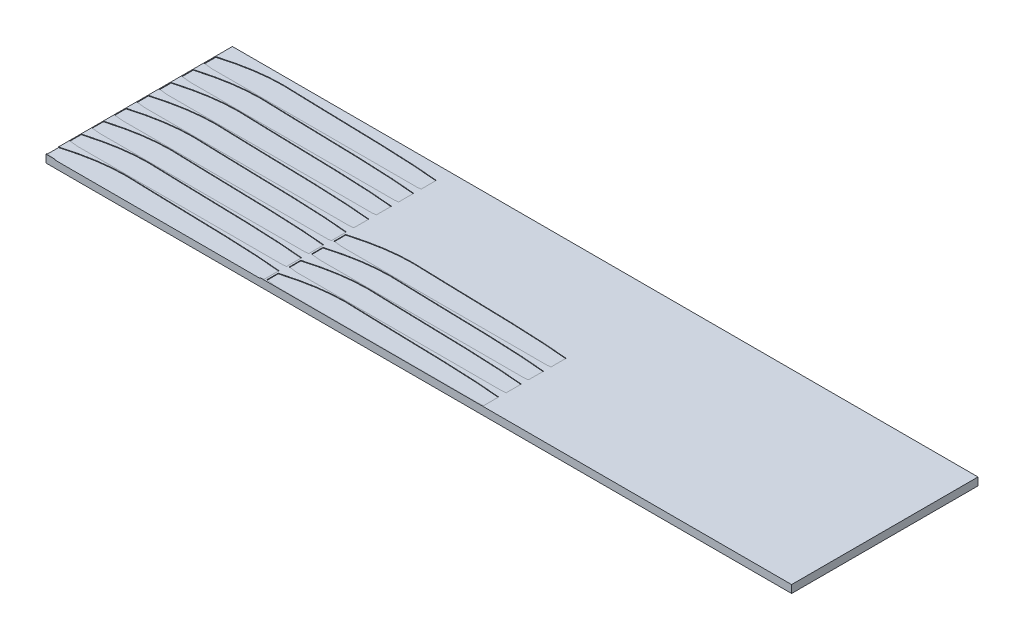
SolidWorks part; units mm, degrees
ref_plane "Front Plane" through (0, 0, 0) normal (0, 0, 1) x (1, 0, 0)
ref_plane "Top Plane" through (0, 0, 0) normal (0, 1, 0) x (1, 0, 0)
ref_plane "Right Plane" through (0, 0, 0) normal (1, 0, 0) x (0, 0, -1)
sketch "Sketch1" plane through (0, 0, 0) normal (0, 1, 0) x (1, 0, 0)
  line L1 (0, 0) -> (-304.8, 0)
  line L2 (0, 0) -> (0, 76.2)
  line L3 (0, 76.2) -> (-304.8, 76.2)
  line L4 (-304.8, 0) -> (-304.8, 76.2)
  dimension "D1" = 304.8
  dimension "D2" = 76.2
extrude "Boss-Extrude1" add sketch "Sketch1" along normal blind 3.175
sketch "Sketch2" plane through (0, 3.175, 0) normal (0, 1, 0) x (1, 0, 0)
  line L0 (-304.8, 76.2) -> (-304.8, 0) construction
  line L1 (-304.8, 6.35) -> (-215.9, 6.35) construction
  line L2 (-304.8, 6.35) -> (-304.8, 0) construction
  line L3 (-304.8, 0) -> (-215.9, 0) construction
  line L4 (-215.9, 6.35) -> (-215.9, 0) construction
  line L5 (-304.8, 0) -> (0, 0) construction
  line L6 (-304.8, 6.35) -> (-311.15, 6.35) construction
  line L7 (-311.15, 6.35) -> (-311.15, 0) construction
  line L8 (-311.15, 0) -> (-304.8, 0) construction
  line L9 (-215.9, 6.35) -> (-209.55, 6.35) construction
  line L10 (-209.55, 6.35) -> (-209.55, 0) construction
  line L11 (-209.55, 0) -> (-215.9, 0) construction
  line L12 (-304.8, 5.1324) -> (-304.8, 0.3904)
  line L13 (-215.9, 0.2103) -> (-215.9, 6.35)
  line L14 (-301.1367, 0) -> (-217.3799, 0)
  line L15 (-304.7482, 14.32) -> (-304.7482, 9.5781)
  line L16 (-215.8482, 9.3979) -> (-215.8482, 15.5376)
  line L17 (-301.0849, 9.1876) -> (-217.3281, 9.1876)
  line L18 (-304.7756, 23.4355) -> (-304.7756, 18.6936)
  line L19 (-215.8756, 18.5134) -> (-215.8756, 24.6532)
  line L20 (-301.1123, 18.3032) -> (-217.3555, 18.3032)
  line L21 (-304.7238, 32.6232) -> (-304.7238, 27.8813)
  line L22 (-215.8238, 27.7011) -> (-215.8238, 33.8408)
  line L23 (-301.0605, 27.4908) -> (-217.3037, 27.4908)
  line L24 (-304.6921, 41.752) -> (-304.6921, 37.0101)
  line L25 (-215.7921, 36.8299) -> (-215.7921, 42.9697)
  line L26 (-301.0288, 36.6197) -> (-217.272, 36.6197)
  line L27 (-304.6403, 50.9397) -> (-304.6403, 46.1977)
  line L28 (-215.7403, 46.0176) -> (-215.7403, 52.1573)
  line L29 (-300.977, 45.8073) -> (-217.2202, 45.8073)
  line L30 (-304.6677, 60.0552) -> (-304.6677, 55.3133)
  line L31 (-215.7677, 55.1331) -> (-215.7677, 61.2729)
  line L32 (-301.0044, 54.9229) -> (-217.2476, 54.9229)
  line L33 (-304.6159, 69.2428) -> (-304.6159, 64.5009)
  line L34 (-215.7159, 64.3207) -> (-215.7159, 70.4605)
  line L35 (-300.9526, 64.1105) -> (-217.1958, 64.1105)
  line L36 (-215.1839, 5.3155) -> (-215.1839, 0.5736)
  line L37 (-126.2839, 0.3934) -> (-126.2839, 6.5331)
  line L38 (-211.5206, 0.1831) -> (-127.7637, 0.1831)
  line L39 (-215.1321, 14.5031) -> (-215.1321, 9.7612)
  line L40 (-126.2321, 9.581) -> (-126.2321, 15.7207)
  line L41 (-211.4688, 9.3707) -> (-127.7119, 9.3707)
  line L42 (-215.1595, 23.6187) -> (-215.1595, 18.8768)
  line L43 (-126.2595, 18.6966) -> (-126.2595, 24.8363)
  line L44 (-211.4962, 18.4863) -> (-127.7393, 18.4863)
  line L45 (-215.1077, 32.8063) -> (-215.1077, 28.0644)
  line L46 (-126.2077, 27.8842) -> (-126.2077, 34.0239)
  line L47 (-211.4444, 27.6739) -> (-127.6875, 27.6739)
  spline S0 degree 3 poles (-304.8, 5.1324) (-295.0561, 7.9134) (-284.6351, 9.1758) (-256.6545, 7.9107) (-231.9837, 8.0391) (-215.9, 6.35) knots 0.033342 0.033342 0.033342 0.033342 0.196819 0.285044 0.915588 0.915588 0.915588 0.915588
  spline S1 degree 3 poles (-304.8, 0.3904) (-303.8212, 0.2292) (-302.6326, 0.1002) (-301.1367, 0) knots 0.767988 0.767988 0.767988 0.767988 1 1 1 1
  spline S2 degree 2 poles (-215.9, 0.2103) (-216.6026, 0.0759) (-217.3799, 0) knots 0.882957 0.882957 0.882957 1 1 1
  spline S3 degree 3 poles (-304.7482, 14.32) (-295.0043, 17.101) (-284.5833, 18.3634) (-256.6027, 17.0983) (-231.9319, 17.2267) (-215.8482, 15.5376) knots 0.033342 0.033342 0.033342 0.033342 0.196819 0.285044 0.915588 0.915588 0.915588 0.915588
  spline S4 degree 3 poles (-304.7482, 9.5781) (-303.7694, 9.4169) (-302.5808, 9.2879) (-301.0849, 9.1876) knots 0.767988 0.767988 0.767988 0.767988 1 1 1 1
  spline S5 degree 2 poles (-215.8482, 9.3979) (-216.5508, 9.2635) (-217.3281, 9.1876) knots 0.882957 0.882957 0.882957 1 1 1
  spline S6 degree 3 poles (-304.7756, 23.4355) (-295.0317, 26.2166) (-284.6108, 27.479) (-256.6301, 26.2139) (-231.9593, 26.3423) (-215.8756, 24.6532) knots 0.033342 0.033342 0.033342 0.033342 0.196819 0.285044 0.915588 0.915588 0.915588 0.915588
  spline S7 degree 3 poles (-304.7756, 18.6936) (-303.7969, 18.5324) (-302.6082, 18.4034) (-301.1123, 18.3032) knots 0.767988 0.767988 0.767988 0.767988 1 1 1 1
  spline S8 degree 2 poles (-215.8756, 18.5134) (-216.5782, 18.3791) (-217.3555, 18.3032) knots 0.882957 0.882957 0.882957 1 1 1
  spline S9 degree 3 poles (-304.7238, 32.6232) (-294.9799, 35.4042) (-284.5589, 36.6666) (-256.5783, 35.4015) (-231.9075, 35.5299) (-215.8238, 33.8408) knots 0.033342 0.033342 0.033342 0.033342 0.196819 0.285044 0.915588 0.915588 0.915588 0.915588
  spline S10 degree 3 poles (-304.7238, 27.8813) (-303.745, 27.72) (-302.5564, 27.591) (-301.0605, 27.4908) knots 0.767988 0.767988 0.767988 0.767988 1 1 1 1
  spline S11 degree 2 poles (-215.8238, 27.7011) (-216.5264, 27.5667) (-217.3037, 27.4908) knots 0.882957 0.882957 0.882957 1 1 1
  spline S12 degree 3 poles (-304.6921, 41.752) (-294.9482, 44.5331) (-284.5273, 45.7954) (-256.5466, 44.5304) (-231.8758, 44.6587) (-215.7921, 42.9697) knots 0.033342 0.033342 0.033342 0.033342 0.196819 0.285044 0.915588 0.915588 0.915588 0.915588
  spline S13 degree 3 poles (-304.6921, 37.0101) (-303.7134, 36.8489) (-302.5247, 36.7199) (-301.0288, 36.6197) knots 0.767988 0.767988 0.767988 0.767988 1 1 1 1
  spline S14 degree 2 poles (-215.7921, 36.8299) (-216.4947, 36.6956) (-217.272, 36.6197) knots 0.882957 0.882957 0.882957 1 1 1
  spline S15 degree 3 poles (-304.6403, 50.9397) (-294.8964, 53.7207) (-284.4755, 54.9831) (-256.4948, 53.718) (-231.824, 53.8464) (-215.7403, 52.1573) knots 0.033342 0.033342 0.033342 0.033342 0.196819 0.285044 0.915588 0.915588 0.915588 0.915588
  spline S16 degree 3 poles (-304.6403, 46.1977) (-303.6616, 46.0365) (-302.4729, 45.9075) (-300.977, 45.8073) knots 0.767988 0.767988 0.767988 0.767988 1 1 1 1
  spline S17 degree 2 poles (-215.7403, 46.0176) (-216.4429, 45.8832) (-217.2202, 45.8073) knots 0.882957 0.882957 0.882957 1 1 1
  spline S18 degree 3 poles (-304.6677, 60.0552) (-294.9238, 62.8363) (-284.5029, 64.0986) (-256.5222, 62.8336) (-231.8514, 62.9619) (-215.7677, 61.2729) knots 0.033342 0.033342 0.033342 0.033342 0.196819 0.285044 0.915588 0.915588 0.915588 0.915588
  spline S19 degree 3 poles (-304.6677, 55.3133) (-303.689, 55.1521) (-302.5003, 55.0231) (-301.0044, 54.9229) knots 0.767988 0.767988 0.767988 0.767988 1 1 1 1
  spline S20 degree 2 poles (-215.7677, 55.1331) (-216.4703, 54.9988) (-217.2476, 54.9229) knots 0.882957 0.882957 0.882957 1 1 1
  spline S21 degree 3 poles (-304.6159, 69.2428) (-294.872, 72.0239) (-284.4511, 73.2863) (-256.4704, 72.0212) (-231.7996, 72.1496) (-215.7159, 70.4605) knots 0.033342 0.033342 0.033342 0.033342 0.196819 0.285044 0.915588 0.915588 0.915588 0.915588
  spline S22 degree 3 poles (-304.6159, 64.5009) (-303.6372, 64.3397) (-302.4485, 64.2107) (-300.9526, 64.1105) knots 0.767988 0.767988 0.767988 0.767988 1 1 1 1
  spline S23 degree 2 poles (-215.7159, 64.3207) (-216.4185, 64.1864) (-217.1958, 64.1105) knots 0.882957 0.882957 0.882957 1 1 1
  spline S24 degree 3 poles (-215.1839, 5.3155) (-205.4399, 8.0965) (-195.019, 9.3589) (-167.0384, 8.0938) (-142.3676, 8.2222) (-126.2839, 6.5331) knots 0.033342 0.033342 0.033342 0.033342 0.196819 0.285044 0.915588 0.915588 0.915588 0.915588
  spline S25 degree 3 poles (-215.1839, 0.5736) (-214.2051, 0.4124) (-213.0165, 0.2834) (-211.5206, 0.1831) knots 0.767988 0.767988 0.767988 0.767988 1 1 1 1
  spline S26 degree 2 poles (-126.2839, 0.3934) (-126.9865, 0.2591) (-127.7637, 0.1831) knots 0.882957 0.882957 0.882957 1 1 1
  spline S27 degree 3 poles (-215.1321, 14.5031) (-205.3881, 17.2842) (-194.9672, 18.5465) (-166.9866, 17.2815) (-142.3158, 17.4098) (-126.2321, 15.7207) knots 0.033342 0.033342 0.033342 0.033342 0.196819 0.285044 0.915588 0.915588 0.915588 0.915588
  spline S28 degree 3 poles (-215.1321, 9.7612) (-214.1533, 9.6) (-212.9646, 9.471) (-211.4688, 9.3707) knots 0.767988 0.767988 0.767988 0.767988 1 1 1 1
  spline S29 degree 2 poles (-126.2321, 9.581) (-126.9347, 9.4467) (-127.7119, 9.3707) knots 0.882957 0.882957 0.882957 1 1 1
  spline S30 degree 3 poles (-215.1595, 23.6187) (-205.4155, 26.3997) (-194.9946, 27.6621) (-167.014, 26.397) (-142.3432, 26.5254) (-126.2595, 24.8363) knots 0.033342 0.033342 0.033342 0.033342 0.196819 0.285044 0.915588 0.915588 0.915588 0.915588
  spline S31 degree 3 poles (-215.1595, 18.8768) (-214.1807, 18.7155) (-212.9921, 18.5866) (-211.4962, 18.4863) knots 0.767988 0.767988 0.767988 0.767988 1 1 1 1
  spline S32 degree 2 poles (-126.2595, 18.6966) (-126.9621, 18.5622) (-127.7393, 18.4863) knots 0.882957 0.882957 0.882957 1 1 1
  spline S33 degree 3 poles (-215.1077, 32.8063) (-205.3637, 35.5874) (-194.9428, 36.8497) (-166.9622, 35.5847) (-142.2914, 35.713) (-126.2077, 34.0239) knots 0.033342 0.033342 0.033342 0.033342 0.196819 0.285044 0.915588 0.915588 0.915588 0.915588
  spline S34 degree 3 poles (-215.1077, 28.0644) (-214.1289, 27.9032) (-212.9403, 27.7742) (-211.4444, 27.6739) knots 0.767988 0.767988 0.767988 0.767988 1 1 1 1
  spline S35 degree 2 poles (-126.2077, 27.8842) (-126.9103, 27.7499) (-127.6875, 27.6739) knots 0.882957 0.882957 0.882957 1 1 1
  dimension "D1" = 88.9
  dimension "D2" = 6.35
  dimension "D3" = 6.35
  dimension "D4" = 6.35
  dimension "D5" = 2.54
  dimension "D6" = 30.48
extrude "Cut-Extrude3" cut sketch "Sketch2" against normal blind 0.254
sketch "Sketch3" plane through (0, 3.175, 0) normal (0, 1, 0) x (1, 0, 0)
  line L0 (-217.3799, 0) -> (0, 0) construction
  line L1 (-124.7737, 0) -> (-73.9737, 0)
  line L2 (-124.7737, 0) -> (-124.7737, 5.588)
  line L4 (-73.9737, 0) -> (-73.9737, 5.715)
  line L5 (-124.6661, 9.5552) -> (-73.8661, 9.5552)
  line L6 (-124.6661, 9.5552) -> (-124.6661, 15.1432)
  line L7 (-73.8661, 9.5552) -> (-73.8661, 15.2702)
  line L8 (-124.6661, 15.1432) -> (-124.6661, 9.5552)
  line L9 (-124.7737, 5.588) -> (-124.7737, 0)
  line L10 (-73.9737, 5.715) -> (-73.9737, 0)
  line L11 (-73.8661, 15.2702) -> (-73.8661, 9.5552)
  line L12 (-124.6047, 19.1295) -> (-73.8047, 19.1295)
  line L13 (-124.6047, 19.1295) -> (-124.6047, 24.7175)
  line L14 (-73.8047, 19.1295) -> (-73.8047, 24.8445)
  line L15 (-124.6047, 24.7175) -> (-124.6047, 19.1295)
  line L16 (-73.8047, 24.8445) -> (-73.8047, 19.1295)
  line L17 (-124.4952, 28.7633) -> (-73.6952, 28.7633)
  line L18 (-124.4952, 28.7633) -> (-124.4952, 34.3513)
  line L19 (-73.6952, 28.7633) -> (-73.6952, 34.4783)
  line L20 (-124.4952, 34.3513) -> (-124.4952, 28.7633)
  line L21 (-73.6952, 34.4783) -> (-73.6952, 28.7633)
  line L22 (-124.3858, 38.3971) -> (-73.5858, 38.3971)
  line L23 (-124.3858, 38.3971) -> (-124.3858, 43.9851)
  line L24 (-73.5858, 38.3971) -> (-73.5858, 44.1121)
  line L25 (-124.3858, 43.9851) -> (-124.3858, 38.3971)
  line L26 (-73.5858, 44.1121) -> (-73.5858, 38.3971)
  line L27 (-124.1668, 49.2351) -> (-73.3668, 49.2351)
  line L28 (-124.1668, 49.2351) -> (-124.1668, 54.8231)
  line L29 (-73.3668, 49.2351) -> (-73.3668, 54.9501)
  line L30 (-124.1668, 54.8231) -> (-124.1668, 49.2351)
  line L31 (-73.3668, 54.9501) -> (-73.3668, 49.2351)
  line L32 (-124.1389, 59.0137) -> (-73.3389, 59.0137)
  line L33 (-124.1389, 59.0137) -> (-124.1389, 64.6017)
  line L34 (-73.3389, 59.0137) -> (-73.3389, 64.7287)
  line L35 (-124.1389, 64.6017) -> (-124.1389, 59.0137)
  line L36 (-73.3389, 64.7287) -> (-73.3389, 59.0137)
  line L37 (-213.6694, 38.4491) -> (-162.8694, 38.4491)
  line L38 (-213.6694, 38.4491) -> (-213.6694, 44.0371)
  line L39 (-162.8694, 38.4491) -> (-162.8694, 44.1641)
  line L40 (-213.6694, 44.0371) -> (-213.6694, 38.4491)
  line L41 (-162.8694, 44.1641) -> (-162.8694, 38.4491)
  line L42 (-213.513, 49.2396) -> (-162.713, 49.2396)
  line L43 (-213.513, 49.2396) -> (-213.513, 54.8276)
  line L44 (-162.713, 49.2396) -> (-162.713, 54.9546)
  line L45 (-213.513, 54.8276) -> (-213.513, 49.2396)
  line L46 (-162.713, 54.9546) -> (-162.713, 49.2396)
  line L47 (-213.2002, 60.0302) -> (-162.4002, 60.0302)
  line L48 (-213.2002, 60.0302) -> (-213.2002, 65.6182)
  line L49 (-162.4002, 60.0302) -> (-162.4002, 65.7452)
  line L50 (-213.2002, 65.6182) -> (-213.2002, 60.0302)
  line L51 (-162.4002, 65.7452) -> (-162.4002, 60.0302)
  line L52 (0, 76.2) -> (-31.75, 76.2)
  line L53 (0, 76.2) -> (-304.8, 76.2) construction
  line L54 (-31.75, 76.2) -> (-63.5, 0)
  line L55 (-63.5, 0) -> (0, 0)
  line L56 (0, 0) -> (0, 76.2)
  spline S0 degree 2 poles (-124.7737, 5.588) (-99.3908, 12.6276) (-73.9737, 5.715) knots 0 0 0 1 1 1
  spline S1 degree 2 poles (-124.6661, 15.1432) (-99.282, 21.6837) (-73.8661, 15.2702) knots 0 0 0 1 1 1
  spline S2 degree 2 poles (-124.6047, 24.7175) (-99.2206, 31.2579) (-73.8047, 24.8445) knots 0 0 0 1 1 1
  spline S3 degree 2 poles (-124.4952, 34.3513) (-99.1112, 40.8917) (-73.6952, 34.4783) knots 0 0 0 1 1 1
  spline S4 degree 2 poles (-124.3858, 43.9851) (-99.0017, 50.5255) (-73.5858, 44.1121) knots 0 0 0 1 1 1
  spline S5 degree 2 poles (-124.1668, 54.8231) (-98.7827, 61.3635) (-73.3668, 54.9501) knots 0 0 0 1 1 1
  spline S6 degree 2 poles (-124.1389, 64.6017) (-98.7548, 71.1422) (-73.3389, 64.7287) knots 0 0 0 1 1 1
  spline S7 degree 2 poles (-213.6694, 44.0371) (-188.2853, 50.5775) (-162.8694, 44.1641) knots 0 0 0 1 1 1
  spline S8 degree 2 poles (-213.513, 54.8276) (-188.1289, 61.3681) (-162.713, 54.9546) knots 0 0 0 1 1 1
  spline S9 degree 2 poles (-213.2002, 65.6182) (-187.8162, 72.1587) (-162.4002, 65.7452) knots 0 0 0 1 1 1
  dimension "D1" = 5.588
  dimension "D2" = 5.715
  dimension "D3" = 5.588
  dimension "D4" = 5.715
  dimension "D5" = 5.588
  dimension "D6" = 5.715
  dimension "D7" = 5.588
  dimension "D8" = 5.715
  dimension "D9" = 5.588
  dimension "D10" = 5.715
  dimension "D11" = 5.588
  dimension "D12" = 5.715
  dimension "D13" = 5.588
  dimension "D14" = 5.715
  dimension "D15" = 5.588
  dimension "D16" = 5.715
  dimension "D17" = 5.588
  dimension "D18" = 5.715
  dimension "D19" = 5.588
  dimension "D20" = 5.715
  dimension "D21" = 31.75
  dimension "D22" = 63.5
